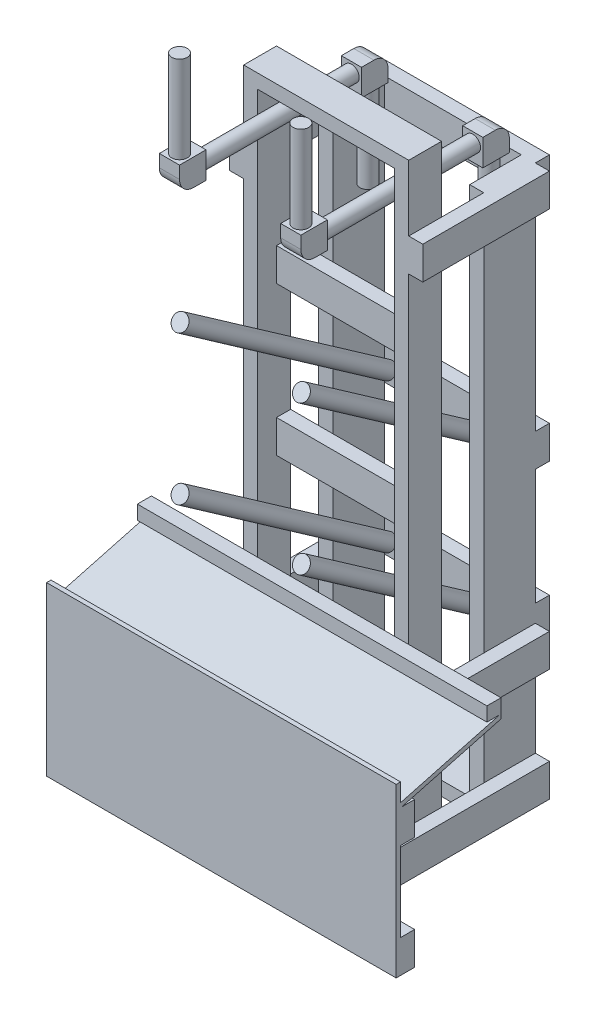
SolidWorks part; units mm, degrees
ref_plane "Front Plane" through (0, 0, 0) normal (0, 0, 1) x (1, 0, 0)
ref_plane "Top Plane" through (0, 0, 0) normal (0, 1, 0) x (1, 0, 0)
ref_plane "Right Plane" through (0, 0, 0) normal (1, 0, 0) x (0, 0, -1)
sketch "TOP LAYOUT" plane through (0, 0, 0) normal (0, 1, 0) x (1, 0, 0)
  line L0 (-480.2035, -831.7368) -> (0, 0) construction
  line L1 (480.2035, -831.7368) -> (960.407, 0)
  line L2 (960.407, 0) -> (480.2035, 831.7368)
  line L3 (480.2035, 831.7368) -> (-480.2035, 831.7368)
  line L4 (-480.2035, 831.7368) -> (-960.407, 0)
  line L5 (-960.407, 0) -> (-480.2035, -831.7368)
  line L6 (-480.2035, -831.7368) -> (480.2035, -831.7368)
  line L7 (473.3294, -819.8306) -> (946.6588, 0)
  line L8 (946.6588, 0) -> (473.3294, 819.8306)
  line L9 (473.3294, 819.8306) -> (-473.3294, 819.8306)
  line L10 (-473.3294, 819.8306) -> (-946.6588, 0)
  line L11 (-946.6588, 0) -> (-473.3294, -819.8306)
  line L12 (-473.3294, -819.8306) -> (473.3294, -819.8306)
  line L13 (0, 0) -> (480.2035, -831.7368) construction
  line L14 (-720.3052, -415.8684) -> (0, 0) construction
  line L15 (0, 0) -> (720.3052, -415.8684) construction
  circle A0 centre (0, 0) radius 831.7368 construction
  circle A1 centre (0, 0) radius 819.8306 construction
  dimension "D1" = 1663.4737
  dimension "D2" = 11.9062
sketch "SIDE LAYOUT" plane through (0, 0, 0) normal (1, 0, 0) x (0, 0, -1)
  line L0 (-767.162, 807.0473) -> (-204.9322, 413.3697)
  line L1 (-767.162, 807.0473) -> (-791.3462, 772.5085)
  line L2 (-204.9322, 413.3697) -> (-229.1165, 378.831)
  line L3 (-791.3462, 772.5085) -> (-229.1165, 378.831)
  line L4 (-767.162, 1210.147) -> (-204.9322, 816.4695)
  line L5 (-767.162, 1210.147) -> (-791.3462, 1175.6083)
  line L6 (-204.9322, 816.4695) -> (-229.1165, 781.9308)
  line L7 (-791.3462, 1175.6083) -> (-229.1165, 781.9308)
  line L8 (-779.2541, 789.7779) -> (-217.0243, 396.1004) construction
  line L9 (-779.2541, 1192.8777) -> (-217.0243, 799.2001) construction
  line L10 (-819.8306, 405.1386) -> (-550.9138, 477.1947)
  line L11 (-779.2541, 789.7779) -> (-779.2541, 1192.8777) construction
  line L12 (-831.7368, 0) -> (-819.8306, 0)
  line L13 (-780.7502, 1825.4878) -> (-780.7502, 1571.4878) construction
  line L14 (-801.8322, 1825.4878) -> (-759.6682, 1825.4878)
  line L15 (-801.8322, 1825.4878) -> (-801.8322, 1571.4878)
  line L16 (-801.8322, 1571.4878) -> (-759.6682, 1571.4878)
  line L17 (-759.6682, 1825.4878) -> (-759.6682, 1571.4878)
  line L18 (-754.3342, 1566.1538) -> (-297.1342, 1566.1538)
  line L19 (-754.3342, 1566.1538) -> (-754.3342, 1523.9898)
  line L20 (-754.3342, 1523.9898) -> (-297.1342, 1523.9898)
  line L21 (-297.1342, 1566.1538) -> (-297.1342, 1523.9898)
  line L22 (-291.8002, 1518.6558) -> (-249.6362, 1518.6558)
  line L23 (-291.8002, 1518.6558) -> (-291.8002, 1264.6558)
  line L24 (-291.8002, 1264.6558) -> (-249.6362, 1264.6558)
  line L25 (-249.6362, 1518.6558) -> (-249.6362, 1264.6558)
  line L26 (-754.3342, 1545.0718) -> (-297.1342, 1545.0718) construction
  line L27 (-270.7182, 1518.6558) -> (-270.7182, 1264.6558) construction
  line L28 (-780.7502, 1571.4878) -> (-780.7502, 1545.0718) construction
  line L29 (-780.7502, 1545.0718) -> (-754.3342, 1545.0718) construction
  line L30 (-297.1342, 1545.0718) -> (-270.7182, 1545.0718) construction
  line L31 (-270.7182, 1545.0718) -> (-270.7182, 1518.6558) construction
  line L32 (-808.0552, 1517.7668) -> (-808.0552, 0) construction
  line L33 (-808.0552, 1589.5218) -> (-736.3002, 1589.5218)
  line L34 (-808.0552, 1589.5218) -> (-808.0552, 1517.7668)
  line L35 (-808.0552, 1517.7668) -> (-736.3002, 1517.7668)
  line L36 (-736.3002, 1589.5218) -> (-736.3002, 1517.7668)
  line L37 (-315.1682, 1572.3768) -> (-243.4132, 1572.3768)
  line L38 (-315.1682, 1572.3768) -> (-315.1682, 1500.6218)
  line L39 (-315.1682, 1500.6218) -> (-243.4132, 1500.6218)
  line L40 (-243.4132, 1572.3768) -> (-243.4132, 1500.6218)
  line L41 (-317.9653, 397.0127) -> (-252.4055, 490.6418)
  line L42 (-547.8322, 1651) -> (-458.9322, 1651)
  line L43 (-547.8322, 1651) -> (-547.8322, 0)
  line L44 (-547.8322, 0) -> (-458.9322, 0)
  line L45 (-458.9322, 1651) -> (-458.9322, 0)
  line L46 (-344.6322, 1473.2) -> (-204.9322, 1473.2)
  line L47 (-344.6322, 1473.2) -> (-344.6322, 0)
  line L48 (-344.6322, 0) -> (-204.9322, 0)
  line L49 (-204.9322, 1473.2) -> (-204.9322, 0)
  line L50 (-317.9653, 397.0127) -> (-297.1589, 382.4439)
  line L51 (-252.4055, 490.6418) -> (-231.5991, 476.073)
  line L52 (-297.1589, 382.4439) -> (-231.5991, 476.073)
  line L53 (-252.4055, 490.6418) -> (-297.1589, 382.4439) construction
  line L54 (-274.7822, 436.5429) -> (-274.7822, 0) construction
  line L55 (-831.7368, 0) -> (-831.7368, 454.025)
  line L56 (-503.3822, 1651) -> (-503.3822, 1545.0718) construction
  line L57 (-327.8682, 1308.1) -> (-213.5682, 1308.1)
  line L58 (-327.8682, 1308.1) -> (-327.8682, 1333.5)
  line L59 (-327.8682, 1333.5) -> (-213.5682, 1333.5)
  line L60 (-213.5682, 1308.1) -> (-213.5682, 1333.5)
  line L61 (-327.8682, 1308.1) -> (-213.5682, 1333.5) construction
  line L62 (-327.8682, 1333.5) -> (-213.5682, 1308.1) construction
  line L63 (-516.0822, 1602.2218) -> (-490.6822, 1602.2218)
  line L64 (-516.0822, 1602.2218) -> (-516.0822, 1487.9218)
  line L65 (-516.0822, 1487.9218) -> (-490.6822, 1487.9218)
  line L66 (-490.6822, 1602.2218) -> (-490.6822, 1487.9218)
  line L67 (-516.0822, 1602.2218) -> (-490.6822, 1487.9218) construction
  line L68 (-516.0822, 1487.9218) -> (-490.6822, 1602.2218) construction
  line L69 (-503.3822, 0) -> (-503.3822, 596.6103) construction
  line L70 (-546.5653, 557.0802) -> (-481.0055, 650.7093)
  line L71 (-546.5653, 557.0802) -> (-525.7589, 542.5113)
  line L72 (-481.0055, 650.7093) -> (-460.1991, 636.1404)
  line L73 (-525.7589, 542.5113) -> (-460.1991, 636.1404)
  line L74 (-546.5653, 557.0802) -> (-460.1991, 636.1404) construction
  line L75 (-481.0055, 650.7093) -> (-525.7589, 542.5113) construction
  line L76 (-204.9322, 843.6501) -> (-166.8322, 843.6501)
  line L77 (-166.8322, 843.6501) -> (-166.8322, 754.7501)
  line L78 (-166.8322, 754.7501) -> (-204.9322, 754.7501)
  line L79 (-204.9322, 440.5504) -> (-166.8322, 440.5504)
  line L80 (-166.8322, 440.5504) -> (-166.8322, 351.6504)
  line L81 (-166.8322, 351.6504) -> (-204.9322, 351.6504)
  line L82 (-217.0243, 799.2001) -> (-166.8322, 799.2001) construction
  line L83 (-217.0243, 396.1004) -> (-166.8322, 396.1004) construction
  line L84 (-831.7368, 1825.4878) -> (-831.7368, 0) construction
  line L85 (-831.7368, 454.025) -> (-819.8306, 454.025)
  line L86 (-819.8306, 0) -> (-819.8306, 454.025)
  line L87 (-819.8306, 405.1386) -> (-816.749, 393.6381)
  line L88 (-550.9138, 477.1947) -> (-547.8322, 465.6941)
  line L89 (-816.749, 393.6381) -> (-547.8322, 465.6941)
  line L90 (-819.8306, 393.6381) -> (-781.7306, 393.6381)
  line L91 (-781.7306, 393.6381) -> (-781.7306, 304.7381)
  line L92 (-781.7306, 304.7381) -> (-819.8306, 304.7381)
  line L93 (-547.8322, 515.2947) -> (-585.9322, 515.2947)
  line L94 (-585.9322, 515.2947) -> (-585.9322, 477.1947)
  line L95 (-585.9322, 477.1947) -> (-547.8322, 477.1947)
  line L96 (-458.9322, 1221.0259) -> (-497.0322, 1221.0259)
  line L97 (-497.0322, 1221.0259) -> (-497.0322, 1132.1259)
  line L98 (-497.0322, 1132.1259) -> (-458.9322, 1132.1259)
  line L99 (-458.9322, 817.9261) -> (-497.0322, 817.9261)
  line L100 (-497.0322, 817.9261) -> (-497.0322, 729.0261)
  line L101 (-497.0322, 729.0261) -> (-458.9322, 729.0261)
  circle A0 centre (-679.7375, 906.8587) radius 203.2
  circle A1 centre (-679.7375, 1309.9584) radius 203.2
  point P55 (-274.7822, 436.5429)
  point P58 (-503.3822, 1545.0718)
  point P62 (-816.7355, 405.9679)
  point P65 (-270.7182, 1320.8)
  point P116 (0, 0)
  point P117 (0, 0)
  dimension "D52" = 406.4
  dimension "D1" = 42.164
  dimension "D4" = 789.7779
  dimension "D5" = 403.0998
  dimension "D6" = 632.6102
  dimension "D7" = 1.4961
  dimension "D8" = 27.305
  dimension "D9" = 27.305
  dimension "D10" = 44.45
  dimension "D11" = 44.45
  dimension "D12" = 18.034
  dimension "D13" = 44.45
  dimension "D14" = 44.45
  dimension "D15" = 18.034
  dimension "D16" = 27.305
  dimension "D17" = 27.305
  dimension "D18" = 686.3558
  dimension "D19" = 686.3558
  dimension "D20" = 254
  dimension "D21" = 457.2
  dimension "D22" = 254
  dimension "D23" = 16.7089
  dimension "D24" = 88.9
  dimension "D25" = 139.7
  dimension "D26" = 114.3
  dimension "D27" = 25.4
  dimension "D30" = 243.5141
  dimension "D31" = 114.3
  dimension "D32" = 25.4
  dimension "D33" = 114.3
  dimension "D34" = 114.3
  dimension "D35" = 25.4
  dimension "D36" = 1651
  dimension "D37" = 1473.2
  dimension "D38" = 152.4
  dimension "D39" = 38.1
  dimension "D40" = 88.9
  dimension "D29" = 35
  dimension "D41" = 283.9047
  dimension "D42" = 11.9062
  dimension "D43" = 454.025
  dimension "D44" = 11.9062
  dimension "D45" = 48.0571
  dimension "D46" = 3.0951
  dimension "D47" = 15
  dimension "D48" = 38.1
  dimension "D49" = 88.9
  dimension "D50" = 38.1
  dimension "D51" = 38.1
  dimension "D28" = 52.4827
  dimension "D53" = 906.8587
  dimension "D54" = 403.0998
  dimension "D55" = 151.9993
  dimension "D56" = 38.1
  dimension "D57" = 88.9
ref_plane "Plane2" through (0, 0, 831.7368) normal (0, 0, 1) x (1, 0, 0)
sketch "Sketch1" plane through (0, 0, 831.7368) normal (0, 0, 1) x (1, 0, 0)
  line L1 (-473.3294, 0) -> (473.3294, 0)
  line L2 (-473.3294, 0) -> (-473.3294, 454.025)
  line L3 (-473.3294, 454.025) -> (473.3294, 454.025)
  line L4 (473.3294, 0) -> (473.3294, 454.025)
  dimension "D1" = 454.025
  dimension "D2" = 946.6588
extrude "Boss-Extrude3" add sketch "Sketch1" against normal blind 11.9062
ref_plane "Plane1" through (164.3062, 0, 0) normal (1, 0, 0) x (0, 0, -1)
sketch "Sketch3" plane through (164.3062, 0, 0) normal (1, 0, 0) x (0, 0, -1)
  line L0 (-779.2541, 789.7779) -> (-217.0243, 396.1004)
  line L1 (-779.2541, 789.7779) -> (-767.162, 807.0473)
  line L2 (-217.0243, 396.1004) -> (-204.9322, 413.3697)
  line L3 (-767.162, 807.0473) -> (-204.9322, 413.3697)
  line L4 (-767.162, 807.0473) -> (-791.3462, 772.5085) construction
  line L5 (-767.162, 807.0473) -> (-204.9322, 413.3697) construction
revolve "Revolve1" add sketch "Sketch3" angle 360 about L0
sketch "Sketch4" plane through (164.3062, 0, 0) normal (1, 0, 0) x (0, 0, -1)
  line L0 (-779.2541, 1192.8777) -> (-217.0243, 799.2001)
  line L1 (-779.2541, 1192.8777) -> (-767.162, 1210.147)
  line L2 (-217.0243, 799.2001) -> (-204.9322, 816.4695)
  line L3 (-767.162, 1210.147) -> (-204.9322, 816.4695)
  line L4 (-767.162, 1210.147) -> (-791.3462, 1175.6083) construction
  line L5 (-767.162, 1210.147) -> (-204.9322, 816.4695) construction
revolve "Revolve2" add sketch "Sketch4" angle 360 about L0
sketch "Sketch5" plane through (164.3062, 0, 0) normal (1, 0, 0) x (0, 0, -1)
  line L1 (-780.7502, 1825.4878) -> (-801.8322, 1825.4878)
  line L2 (-780.7502, 1825.4878) -> (-780.7502, 1571.4878)
  line L3 (-780.7502, 1571.4878) -> (-801.8322, 1571.4878)
  line L4 (-801.8322, 1825.4878) -> (-801.8322, 1571.4878)
revolve "Revolve3" add sketch "Sketch5" angle 360 about L2
sketch "Sketch6" plane through (164.3062, 0, 0) normal (1, 0, 0) x (0, 0, -1)
  line L1 (-754.3342, 1566.1538) -> (-297.1342, 1566.1538)
  line L2 (-754.3342, 1566.1538) -> (-754.3342, 1545.0718)
  line L3 (-754.3342, 1545.0718) -> (-297.1342, 1545.0718)
  line L4 (-297.1342, 1566.1538) -> (-297.1342, 1545.0718)
revolve "Revolve4" add sketch "Sketch6" angle 360 about L3
sketch "Sketch7" plane through (164.3062, 0, 0) normal (1, 0, 0) x (0, 0, -1)
  line L1 (-270.7182, 1518.6558) -> (-249.6362, 1518.6558)
  line L2 (-270.7182, 1518.6558) -> (-270.7182, 1264.6558)
  line L3 (-270.7182, 1264.6558) -> (-249.6362, 1264.6558)
  line L4 (-249.6362, 1518.6558) -> (-249.6362, 1264.6558)
revolve "Revolve5" add sketch "Sketch7" angle 360 about L2
sketch "Sketch8" plane through (164.3062, 0, 0) normal (1, 0, 0) x (0, 0, -1)
  line L1 (-736.3002, 1589.5218) -> (-808.0552, 1589.5218)
  line L2 (-736.3002, 1589.5218) -> (-736.3002, 1517.7668)
  line L3 (-736.3002, 1517.7668) -> (-808.0552, 1517.7668)
  line L4 (-808.0552, 1589.5218) -> (-808.0552, 1517.7668)
  line L5 (-243.4132, 1572.3768) -> (-315.1682, 1572.3768)
  line L6 (-243.4132, 1572.3768) -> (-243.4132, 1500.6218)
  line L7 (-243.4132, 1500.6218) -> (-315.1682, 1500.6218)
  line L8 (-315.1682, 1572.3768) -> (-315.1682, 1500.6218)
extrude "Boss-Extrude2" add sketch "Sketch8" along normal mid plane 54.61
fillet "Fillet1" radius 38.1 2 edges at (164.3062, 1572.3768, 243.4132) (164.3062, 1517.7668, 808.0552)
ref_plane "Plane3" through (0, 0, 547.8322) normal (0, 0, 1) x (1, 0, 0)
sketch "Sketch10" plane through (0, 0, 547.8322) normal (0, 0, 1) x (1, 0, 0)
  line L1 (-223.4883, 0) -> (223.4883, 0)
  line L2 (-223.4883, 0) -> (-223.4883, 1651)
  line L3 (-223.4883, 1651) -> (223.4883, 1651)
  line L4 (223.4883, 0) -> (223.4883, 1651)
  line L5 (-185.3883, 1612.9) -> (185.3883, 1612.9)
  line L6 (-185.3883, 1612.9) -> (-185.3883, 38.1)
  line L7 (-185.3883, 38.1) -> (185.3883, 38.1)
  line L8 (185.3883, 1612.9) -> (185.3883, 38.1)
  ellipse E0 centre (164.3062, 789.7779) end of major axis (185.3882, 789.7779) minor radius 17.2694 construction
  ellipse E1 centre (164.3062, 789.7779) end of major axis (185.3882, 789.7779) minor radius 17.2694 construction
  dimension "D1" = 38.1
  dimension "D2" = 38.1
  dimension "D3" = 38.1
  dimension "D4" = 38.1
extrude "Boss-Extrude4" add sketch "Sketch10" against normal up to vertex (88.9 mm away) separate body up to point (0, 0, 458.9322)
ref_plane "Plane4" through (0, 0, 344.6322) normal (0, 0, 1) x (1, 0, 0)
sketch "Sketch11" plane through (0, 0, 344.6322) normal (0, 0, 1) x (1, 0, 0)
  line L0 (223.4883, 0) -> (223.4883, 1651) construction
  line L1 (223.4883, 1473.2) -> (185.3883, 1473.2)
  line L2 (223.4883, 1473.2) -> (223.4883, 0)
  line L3 (223.4883, 0) -> (-223.4883, 0)
  line L4 (-223.4883, 1473.2) -> (-223.4883, 0)
  line L6 (185.3883, 1473.2) -> (185.3883, 38.1)
  line L7 (185.3883, 38.1) -> (-185.3883, 38.1)
  line L8 (-185.3883, 1473.2) -> (-185.3883, 38.1)
  line L18 (-185.3883, 1473.2) -> (-223.4883, 1473.2)
  dimension "D1" = 38.1
  dimension "D2" = 38.1
  dimension "D3" = 38.1
extrude "Boss-Extrude5" add sketch "Sketch11" against normal up to vertex (139.7 mm away) separate body up to point (0, 1473.2, 204.9322)
sketch "Sketch12" plane through (473.3294, 0, 0) normal (1, 0, 0) x (0, 0, -1)
  line L0 (-547.8322, 515.2947) -> (-585.9322, 515.2947) construction
  line L1 (-585.9322, 515.2947) -> (-585.9322, 477.1947) construction
  line L2 (-585.9322, 477.1947) -> (-547.8322, 477.1947) construction
  line L3 (-819.8306, 405.1386) -> (-550.9138, 477.1947) construction
  line L4 (-816.749, 393.6381) -> (-547.8322, 465.6941) construction
  line L5 (-781.7306, 304.7381) -> (-819.8306, 304.7381) construction
  line L6 (-781.7306, 393.6381) -> (-781.7306, 304.7381) construction
  line L7 (-819.8306, 393.6381) -> (-781.7306, 393.6381) construction
  line L8 (-547.8322, 515.2947) -> (-585.9322, 515.2947)
  line L9 (-585.9322, 515.2947) -> (-585.9322, 477.1947)
  line L10 (-585.9322, 477.1947) -> (-547.8322, 477.1947)
  line L11 (-819.8306, 405.1386) -> (-550.9138, 477.1947)
  line L12 (-816.749, 393.6381) -> (-547.8322, 465.6941)
  line L13 (-781.7306, 304.7381) -> (-819.8306, 304.7381)
  line L14 (-781.7306, 393.6381) -> (-781.7306, 304.7381)
  line L15 (-819.8306, 393.6381) -> (-781.7306, 393.6381)
  line L16 (-819.8306, 405.1386) -> (-819.8306, 304.7381)
  line L17 (-547.8322, 465.6941) -> (-547.8322, 515.2947)
  line M3 (-819.8306, 0) -> (-819.8306, 454.025)
extrude "Boss-Extrude6" add sketch "Sketch12" against normal up to surface (946.6588 mm away) contours L15 L13 L14 M3 | L12 L17 L10 L11 L15 M3 | L10 L17 L8 L9 up to face at (-473.3294, 227.0125, 825.7837)
sketch "Sketch13" plane through (0, 0, 0) normal (1, 0, 0) x (0, 0, -1)
  line L0 (-204.9322, 0) -> (-204.9322, 1473.2) construction
  line L1 (-204.9322, 440.5504) -> (-166.8322, 440.5504)
  line L2 (-204.9322, 440.5504) -> (-204.9322, 351.6504)
  line L3 (-204.9322, 351.6504) -> (-166.8322, 351.6504)
  line L4 (-166.8322, 440.5504) -> (-166.8322, 351.6504)
  line L5 (-204.9322, 440.5504) -> (-166.8322, 440.5504) construction
  line L6 (-204.9322, 843.6501) -> (-166.8322, 843.6501)
  line L7 (-204.9322, 843.6501) -> (-204.9322, 754.7501)
  line L8 (-204.9322, 754.7501) -> (-166.8322, 754.7501)
  line L9 (-166.8322, 843.6501) -> (-166.8322, 754.7501)
  line L10 (-204.9322, 843.6501) -> (-166.8322, 843.6501) construction
  line L12 (-204.9322, 1473.2) -> (-166.8322, 1473.2)
  line L13 (-204.9322, 1473.2) -> (-204.9322, 1384.3)
  line L14 (-204.9322, 1384.3) -> (-166.8322, 1384.3)
  line L15 (-166.8322, 1473.2) -> (-166.8322, 1384.3)
  dimension "D1" = 38.1
  dimension "D2" = 88.9
  dimension "D3" = 38.1
  dimension "D4" = 88.9
extrude "Boss-Extrude7" add sketch "Sketch13" along normal mid plane 446.9765
sketch "Sketch14" plane through (0, 0, 0) normal (0, -1, 0) x (1, 0, 0)
  line L0 (473.3294, 819.8306) -> (473.3294, 831.7368) construction
  line L1 (-473.3294, 819.8306) -> (473.3294, 819.8306)
  line L2 (-473.3294, 819.8306) -> (-473.3294, 781.7306)
  line L3 (-473.3294, 781.7306) -> (473.3294, 781.7306)
  line L4 (473.3294, 819.8306) -> (473.3294, 781.7306)
  line L5 (-261.5883, 781.7306) -> (-261.5883, 204.9322)
  line L6 (-261.5883, 204.9322) -> (-223.4883, 204.9322)
  line L7 (-223.4883, 204.9322) -> (-223.4883, 781.7306)
  line L8 (261.5883, 781.7306) -> (261.5883, 204.9322)
  line L9 (261.5883, 204.9322) -> (223.4883, 204.9322)
  line L10 (223.4883, 204.9322) -> (223.4883, 781.7306)
  line L14 (-223.4883, 204.9322) -> (223.4883, 204.9322) construction
  line L16 (223.4883, 204.9322) -> (223.4883, 344.6322) construction
  line L17 (-223.4883, 204.9322) -> (-223.4883, 344.6322) construction
  line M10 (-473.3294, 819.8306) -> (473.3294, 819.8306)
  dimension "D1" = 38.1
  dimension "D2" = 38.1
  dimension "D3" = 38.1
extrude "Boss-Extrude8" add sketch "Sketch14" against normal blind 88.9 contours L4 L2 L3 M10 | L6 L7 L3 L5 | L10 L9 L8 L3
sketch "Sketch16" plane through (0, 0, 781.7306) normal (0, 0, -1) x (-1, 0, 0)
  line L0 (473.3294, 393.6381) -> (-473.3294, 393.6381) construction
  line L1 (-261.5883, 393.6381) -> (-223.4883, 393.6381)
  line L2 (-261.5883, 393.6381) -> (-261.5883, 304.7381)
  line L3 (-261.5883, 304.7381) -> (-223.4883, 304.7381)
  line L4 (-223.4883, 393.6381) -> (-223.4883, 304.7381)
  line L5 (473.3294, 304.7381) -> (-473.3294, 304.7381) construction
  line L7 (223.4882, 393.6381) -> (261.5883, 393.6381)
  line L8 (223.4882, 393.6381) -> (223.4882, 304.7381)
  line L9 (223.4882, 304.7381) -> (261.5883, 304.7381)
  line L10 (261.5883, 393.6381) -> (261.5883, 304.7381)
  line L12 (-223.4883, 88.9) -> (-223.4883, 351.6504) construction
  line L13 (223.4882, 351.6504) -> (223.4882, 88.9) construction
  dimension "D1" = 38.1
  dimension "D2" = 38.1
extrude "Boss-Extrude9" add sketch "Sketch16" along normal up to surface (576.7984 mm away) up to face at (0, 153.2001, 204.9322)
sketch "Sketch17" plane through (0, 0, 204.9322) normal (0, 0, -1) x (-1, 0, 0)
  line L1 (-261.5883, 1473.2) -> (-223.4883, 1473.2)
  line L2 (-261.5883, 1473.2) -> (-261.5883, 1384.3)
  line L3 (-261.5883, 1384.3) -> (-223.4883, 1384.3)
  line L4 (-223.4883, 1473.2) -> (-223.4883, 1384.3)
  line L5 (261.5883, 1473.2) -> (223.4882, 1473.2)
  line L6 (261.5883, 1473.2) -> (261.5883, 1384.3)
  line L7 (261.5883, 1384.3) -> (223.4882, 1384.3)
  line L8 (223.4882, 1473.2) -> (223.4882, 1384.3)
  dimension "D1" = 38.1
  dimension "D2" = 88.9
extrude "Boss-Extrude10" add sketch "Sketch17" against normal up to surface (342.9 mm away) up to face at (0, 1073.6223, 547.8322)
sketch "Sketch19" plane through (-185.3883, 0, 0) normal (1, 0, 0) x (0, 0, -1)
  line L0 (-458.9322, 1612.9) -> (-458.9322, 38.1) construction
  line L1 (-458.9322, 1221.0259) -> (-497.0322, 1221.0259)
  line L2 (-458.9322, 1221.0259) -> (-458.9322, 1132.1259)
  line L3 (-458.9322, 1132.1259) -> (-497.0322, 1132.1259)
  line L4 (-497.0322, 1221.0259) -> (-497.0322, 1132.1259)
  line L5 (-458.9322, 1221.0259) -> (-497.0322, 1221.0259) construction
  line L6 (-458.9322, 817.9261) -> (-497.0322, 817.9261)
  line L7 (-458.9322, 817.9261) -> (-458.9322, 729.0261)
  line L8 (-458.9322, 729.0261) -> (-497.0322, 729.0261)
  line L9 (-497.0322, 817.9261) -> (-497.0322, 729.0261)
  line L10 (-497.0322, 1221.0259) -> (-497.0322, 1132.1259) construction
  line L11 (-497.0322, 1132.1259) -> (-458.9322, 1132.1259) construction
  line L12 (-458.9322, 817.9261) -> (-497.0322, 817.9261) construction
  line L13 (-497.0322, 817.9261) -> (-497.0322, 729.0261) construction
  line L14 (-497.0322, 729.0261) -> (-458.9322, 729.0261) construction
extrude "Boss-Extrude11" add sketch "Sketch19" along normal up to surface (370.7765 mm away) up to face at (185.3883, 713.8315, 518.1989)
mirror "Mirror1" about plane through (0, 0, 0) normal (1, 0, 0) of bodies 102 103 107
equation "\"Thick\"= 0.46875in"
equation "\"D2@TOP LAYOUT\" = \"Thick\""
equation "\"D42@SIDE LAYOUT\" = \"Thick\""
equation "\"D1@Boss-Extrude3\"=\"Thick\""
equation "\"D44@SIDE LAYOUT\"=\"Thick\""
